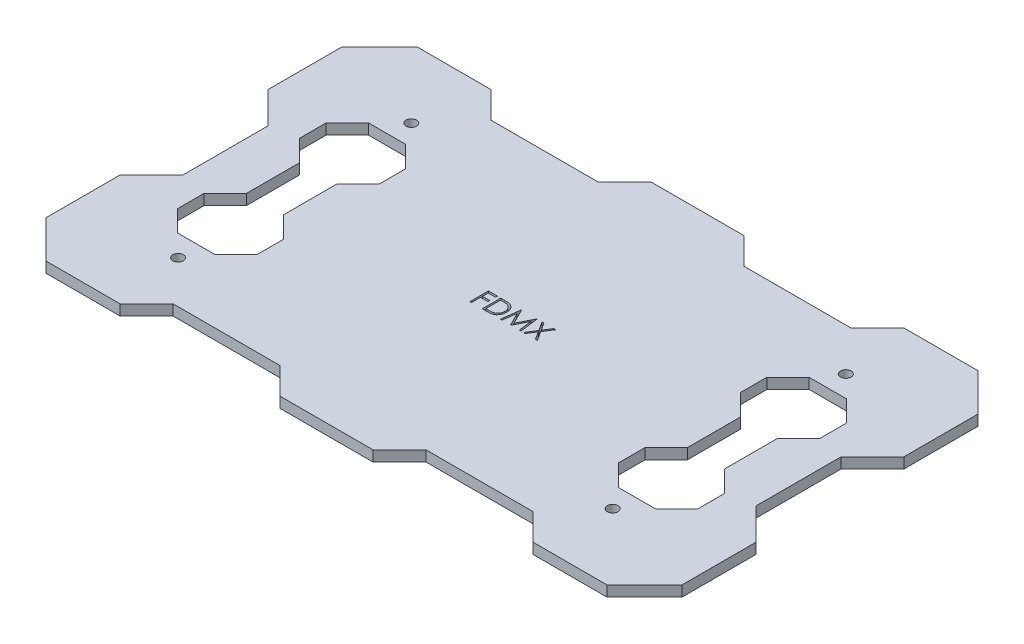
SolidWorks part; units mm, degrees
ref_plane "Front Plane" through (0, 0, 0) normal (0, 0, 1) x (1, 0, 0)
ref_plane "Top Plane" through (0, 0, 0) normal (0, 1, 0) x (1, 0, 0)
ref_plane "Right Plane" through (0, 0, 0) normal (1, 0, 0) x (0, 0, -1)
sketch "Sketch1" plane through (0, 0, 0) normal (0, 1, 0) x (1, 0, 0)
  line L0 (0, 0) -> (-38.0711, 0)
  line L1 (-54.0711, 0) -> (-54.0711, 8)
  line L2 (-54.0711, 8) -> (-60, 13.9289)
  line L3 (-60, 13.9289) -> (-60, 27.9289)
  line L4 (-60, 27.9289) -> (-52.9289, 35)
  line L5 (-52.9289, 35) -> (-38.9289, 35)
  line L6 (-38.9289, 35) -> (-33.9289, 30)
  line L7 (-33.9289, 30) -> (-13.7769, 30)
  line L8 (-13.7769, 30) -> (-8.7769, 35)
  line L9 (-8.7769, 35) -> (0, 35)
  line L10 (0, 35) -> (0, 0)
  line L11 (-45.0711, 0) -> (-45.0711, 5)
  line L12 (-45.0711, 5) -> (-49.0711, 9)
  line L13 (-49.0711, 9) -> (-49.0711, 14)
  line L14 (-49.0711, 14) -> (-45.0711, 18)
  line L15 (-45.0711, 18) -> (-38.0711, 18)
  line L16 (-38.0711, 18) -> (-34.0711, 14)
  line L17 (-34.0711, 14) -> (-34.0711, 9)
  line L18 (-34.0711, 9) -> (-38.0711, 5)
  line L19 (-38.0711, 5) -> (-38.0711, 0)
  line L20 (-49.0711, 9) -> (-34.0711, 9) construction
  line L21 (-49.0711, 14) -> (-34.0711, 14) construction
  line L22 (-45.0711, 5) -> (-38.0711, 5) construction
  line L23 (-54.0711, 0) -> (-45.0711, 0)
  circle A0 centre (-41, 22) radius 1
  dimension "D16" = 22
  dimension "D1" = 45
  dimension "D2" = 14
  dimension "D3" = 8
  dimension "D4" = 10
  dimension "D5" = 14
  dimension "D6" = 60
  dimension "D7" = 35
  dimension "D8" = 5
  dimension "D9" = 5
  dimension "D10" = 7
  dimension "D11" = 18
  dimension "D12" = 5
  dimension "D13" = 9
  dimension "D14" = 4
  dimension "D15" = 5
  dimension "D17" = 41
extrude "Boss-Extrude1" add sketch "Sketch1" along normal blind 2
mirror "Mirror1" about plane through (0, 0, 0) normal (1, 0, 0) of "Boss-Extrude1"
sketch "Sketch3" plane through (0, 2, 0) normal (0, 1, 0) x (1, 0, 0)
  text T0 "FDMX"
extrude "Cut-Extrude2" cut sketch "Sketch3" along a picked direction on the side against the normal blind 2
